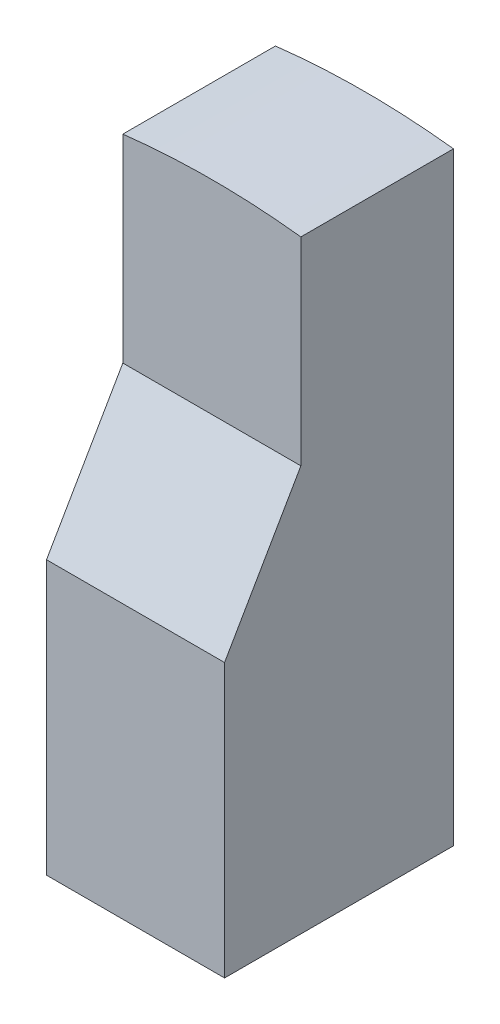
SolidWorks part; units mm, degrees
material "Plain Carbon Steel"
ref_plane "Front Plane" through (0, 0, 0) normal (0, 0, 1) x (1, 0, 0)
ref_plane "Top Plane" through (0, 0, 0) normal (0, 1, 0) x (1, 0, 0)
ref_plane "Right Plane" through (0, 0, 0) normal (1, 0, 0) x (0, 0, -1)
sketch "Sketch1" plane through (0, 0, 0) normal (0, 0, 1) x (1, 0, 0)
  line L0 (0, 63.7083) -> (0, -61.7721) construction
  line L1 (-17.5, 148.9757) -> (-17.5, 30.31)
  line L2 (17.5, 148.9757) -> (17.5, 30.31)
  line L3 (-17.5, 30.31) -> (17.5, 30.31)
  circle A0 centre (0, 0) radius 150 construction
  arc A1 (-17.5, 148.9757) -> (17.5, 148.9757) centre (0, 0) cw
  dimension "D1" = 300
  dimension "D2" = 30.31
  dimension "D3" = 35
extrude "Boss-Extrude1" add sketch "Sketch1" along normal mid plane 45
sketch "Sketch2" plane through (17.5, 0, 0) normal (1, 0, 0) x (0, 0, -1)
  line L0 (-22.5, 84.0192) -> (-7.5, 110)
  line L1 (-22.5, 30.31) -> (-22.5, 148.9757) construction
  line L3 (22.5, 150) -> (-22.5, 150) construction
  line L5 (-22.5, 150) -> (-22.5, 148.9757) construction
  line L6 (-22.5, 150) -> (-22.5, 84.0192)
  line L7 (-22.5, 150) -> (-7.5, 150)
  line L8 (-7.5, 150) -> (-7.5, 110)
  dimension "D1" = 15
  dimension "D2" = 40
  dimension "D3" = 150
extrude "Cut-Extrude1" cut sketch "Sketch2" against normal through all
